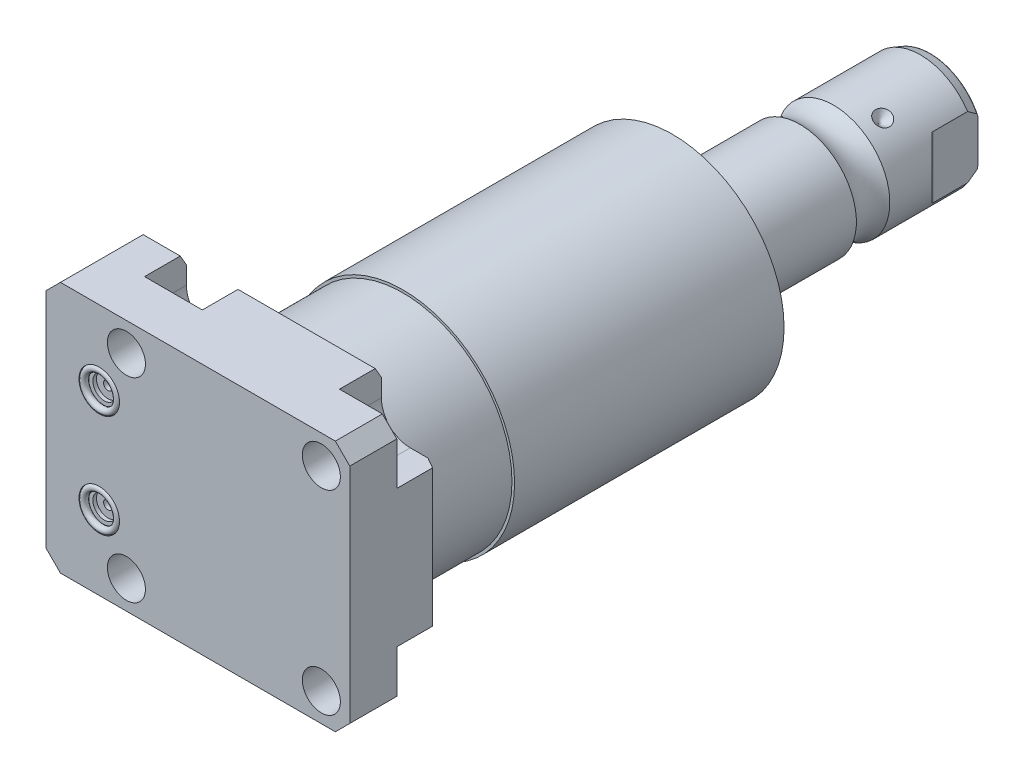
SolidWorks part; units mm, degrees
material "Alloy Steel"
ref_plane "Front Plane" through (0, 0, 0) normal (0, 0, 1) x (1, 0, 0)
ref_plane "Top Plane" through (0, 0, 0) normal (0, 1, 0) x (1, 0, 0)
ref_plane "Right Plane" through (0, 0, 0) normal (1, 0, 0) x (0, 0, -1)
sketch "Sketch1" plane through (0, 0, 0) normal (0, 0, 1) x (1, 0, 0)
  line L0 (-50.063, 35.433) -> (35.433, 35.433)
  line L1 (35.433, 35.433) -> (35.433, -35.433)
  line L2 (35.433, -35.433) -> (-50.063, -35.433)
  line L3 (-50.063, -35.433) -> (-50.063, 35.433)
  dimension "D1" = 85.496
  dimension "D2" = 70.866
  dimension "D3" = 35.433
  dimension "D4" = 35.433
extrude "Extrude1" add sketch "Sketch1" along normal blind 25.019
hole_wizard "Hole1" positions "Sketch22" profile "Sketch21" legacy end condition through all
sketch "Sketch22" plane through (0, 0, 0) normal (0, 0, -1) x (-1, 0, 0)
  line L0 (0, 0) -> (42.7441, 0) construction
  line L1 (0, 0.8532) -> (0, 27.5062) construction
  point P0 (-27.432, -27.432)
  point P9 (-27.432, 27.432)
  point P11 (27.432, 27.432)
  point P12 (27.432, -27.432)
  dimension "D1" = 27.432
  dimension "D2" = 27.432
sketch "Sketch21" plane through (27.432, -27.432, 0) normal (1, 0, 0) x (0, 1, 0)
  line L0 (0, 0) -> (0, 25.019)
  line L1 (0, 25.019) -> (5.3595, 25.019)
  line L2 (5.3595, 25.019) -> (5.3595, 0)
  line L3 (5.3595, 0) -> (0, 0)
  line L4 (0, 110) -> (0, -10) construction
  dimension "Diameter" = 10.719
  dimension "Depth" = 25.019
sketch "Sketch3" plane through (0, 0, 0) normal (0, 0, -1) x (-1, 0, 0)
  line L0 (-27.432, -19.304) -> (-35.433, -19.304)
  line L1 (-35.433, -35.433) -> (-35.433, -19.304)
  line L2 (-35.433, 19.304) -> (-35.433, 35.433)
  line L3 (-35.433, 19.304) -> (-27.432, 19.304)
  line L4 (-19.304, 27.432) -> (-19.304, 35.433)
  line L5 (-35.433, 35.433) -> (-19.304, 35.433)
  line L6 (19.304, 35.433) -> (19.304, 27.432)
  line L7 (35.56, 27.432) -> (35.56, 35.433)
  line L8 (19.304, 35.433) -> (35.56, 35.433)
  line L9 (35.56, -35.433) -> (19.304, -35.433)
  line L10 (35.56, -35.433) -> (35.56, -27.432)
  line L11 (19.304, -27.432) -> (19.304, -35.433)
  line L12 (-19.304, -35.433) -> (-35.433, -35.433)
  line L13 (-19.304, -35.433) -> (-19.304, -27.432)
  line L14 (-35.433, 35.433) -> (50.063, 35.433) construction
  line L15 (-35.433, -35.433) -> (-35.433, 35.433) construction
  line L16 (50.063, -35.433) -> (-35.433, -35.433) construction
  arc A0 (-19.304, -27.432) -> (-27.432, -19.304) centre (-27.432, -27.432) ccw
  arc A1 (-27.432, 19.304) -> (-19.304, 27.432) centre (-27.432, 27.432) ccw
  arc A2 (19.304, 27.432) -> (35.56, 27.432) centre (27.432, 27.432) ccw
  arc A3 (35.56, -27.432) -> (19.304, -27.432) centre (27.432, -27.432) ccw
  circle A8 centre (-27.432, 27.432) radius 5.3595 construction
  circle A9 centre (-27.432, -27.432) radius 5.3595 construction
  circle A10 centre (27.432, -27.432) radius 5.3595 construction
  circle A11 centre (27.432, 27.432) radius 5.3595 construction
  dimension "D1" = 8.128
extrude "Cut-Extrude2" cut sketch "Sketch3" against normal blind 11.786
ref_plane "Plane16" through (0, 0, 12.522) normal (0, 0, 1) x (1, 0, 0)
sketch "Sketch23" plane through (0, 0, 12.522) normal (0, 0, 1) x (1, 0, 0)
  line L0 (-11.9397, -13.0048) -> (-61.0013, -13.0048) construction
  line L1 (-50.063, -23.749) -> (-49.809, -23.749)
  line L3 (-49.809, -23.749) -> (-49.809, -19.6596)
  line L4 (-49.809, -19.6596) -> (-49.0978, -18.9484)
  line L5 (-49.0978, -18.9484) -> (-35.6358, -18.9484)
  line L6 (-35.6358, -18.9484) -> (-35.6358, -13.0048)
  line L7 (-35.6358, -13.0048) -> (-50.063, -13.0048)
  line L8 (-50.063, -13.0048) -> (-50.063, -23.749)
  line L10 (-50.063, 35.433) -> (-50.063, -35.433) construction
  dimension "D1" = 21.4884
  dimension "D2" = 0.254
  dimension "D3" = 45
  dimension "D4" = 13.3096
  dimension "D5" = 11.8872
  dimension "D6" = 14.1732
  dimension "D7" = 13.0048
revolve "Cut-Revolve5" cut sketch "Sketch23" angle 360 about L0
mirror "Mirror1" about plane through (0, 0, 0) normal (0, 1, 0) of "Cut-Revolve5"
sketch "Sketch6" plane through (0, 0, 25.019) normal (0, 0, 1) x (1, 0, 0)
  line L0 (0, 0) -> (-71.0417, 0) construction
  circle A0 centre (-35.077, -14.529) radius 5.7023
  circle A1 centre (-35.077, 14.529) radius 5.7023
  dimension "D4" = 11.4046
  dimension "D1" = 14.529
  dimension "D2" = 29.058
  dimension "D3" = 35.077
extrude "Cut-Extrude3" cut sketch "Sketch6" against normal blind 1.4478
sketch "Sketch7" plane through (0, 0, 23.5712) normal (0, 0, 1) x (1, 0, 0)
  circle A0 centre (-35.077, 14.529) radius 3.2512
  circle A1 centre (-35.077, -14.529) radius 3.2512
  circle A2 centre (-35.077, 14.529) radius 5.7023 construction
  circle A3 centre (-35.077, -14.529) radius 5.7023 construction
  dimension "D1" = 6.5024
extrude "Cut-Extrude4" cut sketch "Sketch7" against normal blind 1.016
sketch "Sketch8" plane through (0, 0, 22.5552) normal (0, 0, 1) x (1, 0, 0)
  circle A0 centre (-35.077, 14.529) radius 1.2446
  circle A1 centre (-35.077, -14.529) radius 1.2446
  circle A2 centre (-35.077, 14.529) radius 5.7023 construction
  circle A3 centre (-35.077, -14.529) radius 5.7023 construction
  dimension "D1" = 2.4892
extrude "Cut-Extrude5" cut sketch "Sketch8" against normal blind 11.9888
ref_plane "Plane17" through (0, 14.5288, 0) normal (0, 1, 0) x (-1, 0, 0)
sketch "Sketch9" plane through (-41.656, 14.5288, 23.5712) normal (0, 1, 0) x (1, 0, 0)
  line L0 (6.579, -1.9469) -> (6.579, 0.0927) construction
  line L3 (0.8767, 0) -> (12.2813, 0) construction
  line L4 (6.579, 13.0048) -> (6.579, 1.016) construction
  circle A0 centre (11.3542, -0.9271) radius 0.9271
  dimension "D1" = 1.8542
  dimension "D2" = 9.5504
revolve "Revolve1" add sketch "Sketch9" angle 360 about L0
mirror "Mirror2" about plane through (0, 0, 0) normal (0, 1, 0) of bodies 116
chamfer "Chamfer1" distance 4.064 angle 45 4 edges at (35.433, -35.433, 18.4025) (35.433, 35.433, 18.4025) (-50.063, 35.433, 12.5095) (-50.063, -35.433, 12.5095)
chamfer "Chamfer2" distance 3.0226 angle 30 5 edges at (-40.7795, -35.433, 0) (0, -35.433, 0) (35.433, 0, 0) (-40.7795, 35.433, 0) (0, 35.433, 0)
sketch "Sketch24" plane through (0, 0, 0) normal (1, 0, 0) x (0, 0, -1)
  line L0 (0, 0) -> (113.9127, 0) construction
  line L1 (0, 0) -> (0, 30.658)
  line L2 (0, 30.658) -> (25.4, 30.658)
  line L3 (25.4, 30.658) -> (25.4, 31.3945)
  line L4 (25.4, 31.3945) -> (101.2423, 31.3945)
  line L5 (101.2423, 31.3945) -> (104.55, 19.05)
  line L6 (104.55, 19.05) -> (104.55, 0)
  line L7 (104.55, 0) -> (0, 0)
  dimension "D1" = 61.316
  dimension "D2" = 25.4
  dimension "D3" = 62.789
  dimension "D4" = 38.1
  dimension "D5" = 15
  dimension "D6" = 104.55
revolve "Revolve4" add sketch "Sketch24" angle 360 about L0
sketch "Sketch17" plane through (0, 0, 0) normal (1, 0, 0) x (0, 0, -1)
  line L0 (104.55, 0) -> (104.55, -15.875)
  line L1 (104.55, -15.875) -> (137.1177, -15.875)
  line L2 (146.5323, -15.875) -> (171.01, -15.875)
  line L3 (173.931, -14.8118) -> (173.931, 0)
  line L4 (173.931, 0) -> (104.55, 0)
  line L5 (130.8989, 0) -> (0.816, 0) construction
  line L6 (104.55, -19.05) -> (104.55, 19.05) construction
  line L7 (-25.019, -31.369) -> (-25.019, 31.369) construction
  line L8 (173.931, -14.8118) -> (171.01, -15.875)
  arc A0 (146.5323, -15.875) -> (137.1177, -15.875) centre (141.825, -22.2505) ccw
  dimension "D2" = 20
  dimension "D4" = 7.925
  dimension "D5" = 28.651
  dimension "D1" = 198.95
  dimension "D3" = 31.75
  dimension "D6" = 32.106
  dimension "D7" = 2.921
revolve "Revolve3" add sketch "Sketch17" angle 360 about L5
sketch "Sketch30" plane through (0, 0, 0) normal (0, 1, 0) x (1, 0, 0)
  line L0 (-27.8193, 152.493) -> (0.6125, 152.493) construction
  line L1 (-15.875, 154.906) -> (-13.462, 152.493)
  line L2 (-15.875, 171.01) -> (-15.875, 146.5323) construction
  line L3 (-13.462, 152.493) -> (-15.875, 152.493)
  line L4 (-15.875, 152.493) -> (-15.875, 154.906)
  arc A0 (-15.875, 137.1177) -> (-15.875, 146.5323) centre (-22.2505, 141.825) ccw construction
  dimension "D1" = 45
  dimension "D2" = 4.826
  dimension "D3" = 10.668
revolve "Cut-Revolve6" cut sketch "Sketch30" angle 360 about L0
pattern_circular "CirPattern1" count 3 over 360 about axis through (0, 0, -130.8989) along (0, 0, -1) of "Cut-Revolve6"
fillet "Fillet2" radius 0.635 1 edges at (-14.8118, 0, -173.931)
sketch "Sketch32" plane through (0, 0, 0) normal (0, 1, 0) x (1, 0, 0)
  line L0 (0, 0) -> (0, 187.7199) construction
  line L1 (-13.284, 173.931) -> (-13.284, 161.231)
  line L2 (14.3672, 173.931) -> (-14.3672, 173.931) construction
  line L3 (-13.5072, 160.6922) -> (-15.875, 158.3244)
  line L4 (-15.875, 171.01) -> (-15.875, 154.906) construction
  line L5 (-15.875, 158.3244) -> (-15.875, 173.931)
  line L6 (-15.875, 173.931) -> (-13.284, 173.931)
  line L7 (15.875, 173.931) -> (13.284, 173.931)
  line L8 (15.875, 158.3244) -> (15.875, 173.931)
  line L9 (13.5072, 160.6922) -> (15.875, 158.3244)
  line L10 (13.284, 173.931) -> (13.284, 161.231)
  arc A0 (-13.284, 161.231) -> (-13.5072, 160.6922) centre (-14.046, 161.231) cw
  arc A1 (13.284, 161.231) -> (13.5072, 160.6922) centre (14.046, 161.231) ccw
  dimension "D1" = 0.762
  dimension "D2" = 12.7
  dimension "D3" = 45
  dimension "D4" = 26.568
extrude "Cut-Extrude8" cut sketch "Sketch32" against normal through all and the other way through all
hole_wizard "Hole2" positions "Sketch34" profile "Sketch33" legacy
sketch "Sketch34" plane through (0, 0, -173.931) normal (0, 0, -1) x (-1, 0, 0)
  circle A0 centre (0, 0) radius 15.875 construction
  point P0 (0, 0)
sketch "Sketch33" plane through (0, 0, -173.931) normal (1, 0, 0) x (0, 1, 0)
  line L0 (0, 0) -> (0, 29.5665)
  line L1 (0, 29.5665) -> (6.9342, 25.4)
  line L2 (6.9342, 25.4) -> (6.9342, 0)
  line L4 (6.9342, 0) -> (0, 0)
  line L6 (0, 29.5665) -> (-6.9342, 25.4) construction
  line L7 (0, -4.2442) -> (0, 117.3081) construction
  dimension "Diameter" = 13.8684
  dimension "Depth" = 25.4
  dimension "Drill Angle" = 118
